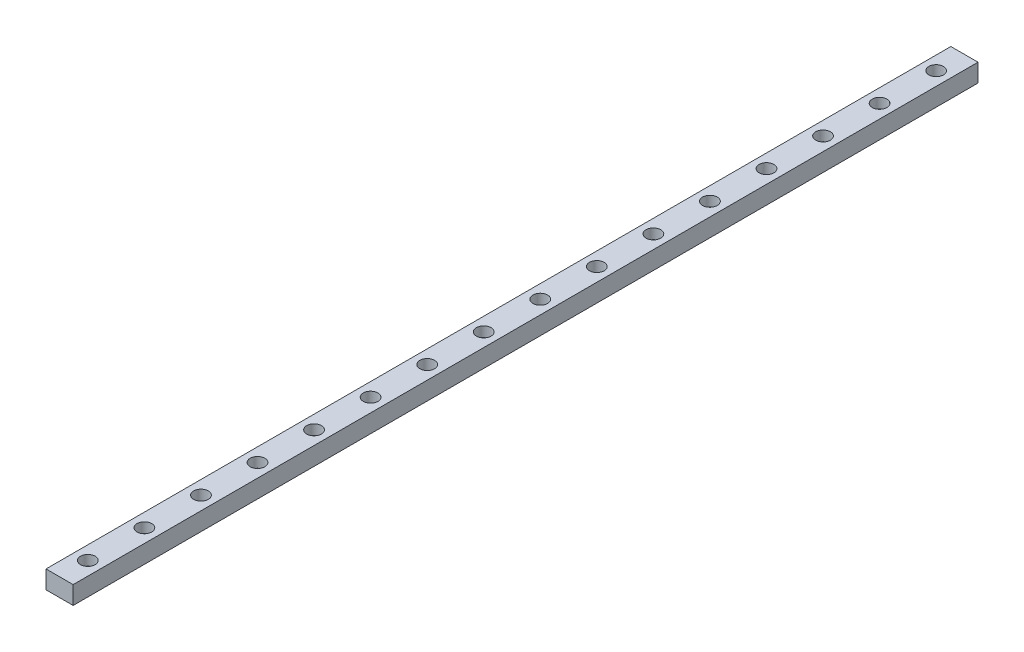
SolidWorks part; units mm, degrees
ref_plane "Front" through (0, 0, 0) normal (0, 0, 1) x (1, 0, 0)
ref_plane "Top" through (0, 0, 0) normal (0, 1, 0) x (1, 0, 0)
ref_plane "Right" through (0, 0, 0) normal (1, 0, 0) x (0, 0, -1)
sketch "Sketch1" plane through (0, 0, 0) normal (0, 0, 1) x (1, 0, 0)
  line L1 (0, 0) -> (12, 0)
  line L2 (0, 0) -> (0, 8)
  line L3 (0, 8) -> (12, 8)
  line L4 (12, 0) -> (12, 8)
  dimension "D1" = 12
  dimension "D2" = 8
extrude "Boss-Extrude1" add sketch "Sketch1" along normal blind 400
hole_wizard "CBORE for M3 SHCS1" positions "Sketch2" profile "Sketch3" counterbore size "M3" standard "ANSI Metric" end condition through all
sketch "Sketch2" plane through (0, 8, 0) normal (0, 1, 0) x (1, 0, 0)
  line L1 (12, -400) -> (0, -400) construction
  point P0 (6, -387.5)
  dimension "D1" = 12.5
sketch "Sketch3" plane through (6, 8, 387.5) normal (1, 0, 0) x (0, 0, 1)
  line L0 (0, 0) -> (0, 8)
  line L1 (0, 8) -> (1.7, 8)
  line L3 (1.7, 8) -> (1.7, 4.5)
  line L4 (1.7, 4.5) -> (3.25, 4.5)
  line L5 (3.25, 4.5) -> (3.25, 0)
  line L7 (3.25, 0) -> (0, 0)
  line L11 (0, -6.35) -> (0, 107.95) construction
  dimension "Thru Hole Dia." = 3.4
  dimension "Thru Hole Depth" = 8
  dimension "C'Bore Dia." = 6.5
  dimension "C'Bore Depth" = 4.5
pattern_linear "LPattern1" count 16 spacing 25 along (0, 0, -1) of "CBORE for M3 SHCS1"
equation "\"length\"=400"
equation "\"D1@Boss-Extrude1\"=\"length\""
